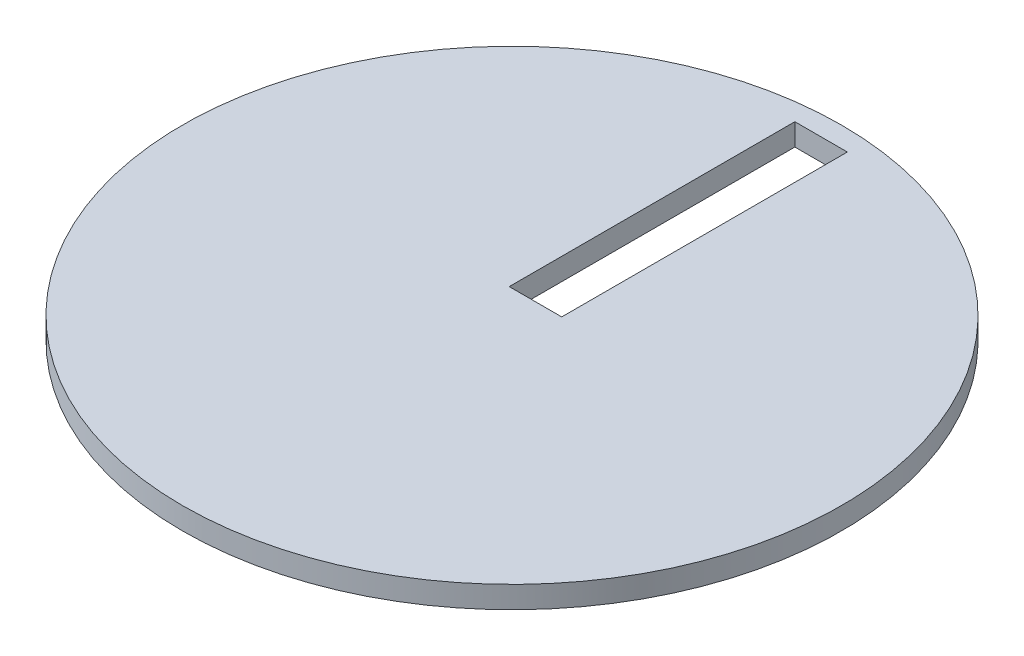
SolidWorks part; units mm, degrees
ref_plane "Front Plane" through (0, 0, 0) normal (0, 0, 1) x (1, 0, 0)
ref_plane "Top Plane" through (0, 0, 0) normal (0, 1, 0) x (1, 0, 0)
ref_plane "Right Plane" through (0, 0, 0) normal (1, 0, 0) x (0, 0, -1)
sketch "Sketch1" plane through (0, 0, 0) normal (0, 1, 0) x (1, 0, 0)
  circle A0 centre (0, 0) radius 150
  dimension "D1" = 300
extrude "Boss-Extrude1" add sketch "Sketch1" along normal blind 10
sketch "Sketch2" plane through (0, 10, 0) normal (0, 1, 0) x (1, 0, 0)
  line L1 (-11.9455, 140.6881) -> (11.9455, 140.6881)
  line L2 (-11.9455, 140.6881) -> (-11.9455, 10.6881)
  line L3 (-11.9455, 10.6881) -> (11.9455, 10.6881)
  line L4 (11.9455, 140.6881) -> (11.9455, 10.6881)
  line L5 (-11.9455, 140.6881) -> (11.9455, 10.6881) construction
  line L6 (-11.9455, 10.6881) -> (11.9455, 140.6881) construction
  point P0 (0, 75.6881)
  dimension "D1" = 130
extrude "Cut-Extrude1" cut sketch "Sketch2" against normal blind 10
